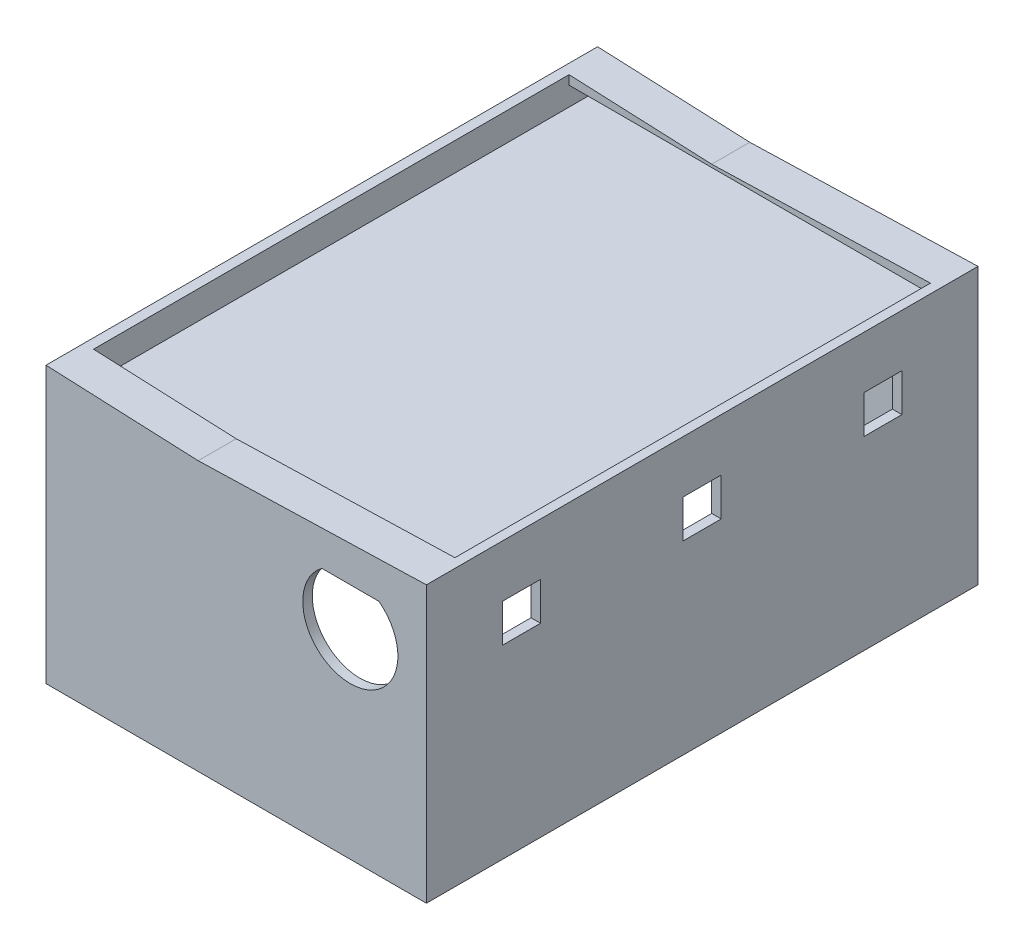
SolidWorks part; units mm, degrees
ref_plane "Front Plane" through (0, 0, 0) normal (0, 0, 1) x (1, 0, 0)
ref_plane "Top Plane" through (0, 0, 0) normal (0, 1, 0) x (1, 0, 0)
ref_plane "Right Plane" through (0, 0, 0) normal (1, 0, 0) x (0, 0, -1)
sketch "Sketch1" plane through (0, 0, 0) normal (0, 1, 0) x (1, 0, 0)
  line L1 (-96.0616, 57.1062) -> (103.9384, 57.1062)
  line L2 (-96.0616, 57.1062) -> (-96.0616, -232.8938)
  line L3 (-96.0616, -232.8938) -> (103.9384, -232.8938)
  line L4 (103.9384, 57.1062) -> (103.9384, -232.8938)
  dimension "D1" = 200
  dimension "D2" = 290
extrude "Boss-Extrude2" add sketch "Sketch1" along normal blind 10 contours L2 L3 L4 L1
sketch "Sketch2" plane through (0, 10, 0) normal (0, 1, 0) x (1, 0, 0)
  line L0 (-96.0616, -87.8938) -> (103.9384, -87.8938)
  line L1 (-96.0616, 57.1062) -> (-96.0616, -232.8938) construction
  line L2 (103.9384, 57.1062) -> (103.9384, -232.8938) construction
  line L3 (3.9384, 57.1062) -> (3.9384, -232.8938)
  line L4 (-96.0616, 57.1062) -> (103.9384, 57.1062) construction
  line L5 (-96.0616, -232.8938) -> (103.9384, -232.8938) construction
  line L7 (-91.0616, 52.1062) -> (98.9384, 52.1062)
  line L8 (-91.0616, 52.1062) -> (-91.0616, -227.8938)
  line L9 (-91.0616, -227.8938) -> (98.9384, -227.8938)
  line L10 (98.9384, 52.1062) -> (98.9384, -227.8938)
  line L11 (-91.0616, 52.1062) -> (98.9384, -227.8938) construction
  line L12 (-91.0616, -227.8938) -> (98.9384, 52.1062) construction
  point P12 (3.9384, -87.8938)
  line M3 (103.9384, 57.1062) -> (-96.0616, 57.1062)
  line M4 (-96.0616, 57.1062) -> (-96.0616, -232.8938)
  line M5 (-96.0616, -232.8938) -> (103.9384, -232.8938)
  line M6 (103.9384, -232.8938) -> (103.9384, 57.1062)
  dimension "D1" = 5
  dimension "D2" = 5
extrude "Boss-Extrude4" add sketch "Sketch2" along normal blind 140 contours L8 L7 L3 L0 M3 M4 | L7 L10 L0 L3 M6 M3 | L0 L10 L9 L3 M5 M6 | L9 L8 L0 L3 M4 M5
sketch "Sketch5" plane through (103.9384, 0, 0) normal (1, 0, 0) x (0, 0, -1)
  line L0 (-232.8938, 75) -> (-232.8938, 112.5)
  line L1 (-232.8938, 150) -> (-232.8938, 0) construction
  line L2 (-232.8938, 112.5) -> (57.1062, 112.5)
  line L3 (57.1062, 150) -> (57.1062, 0) construction
  line L4 (-87.8938, 112.5) -> (-160.3938, 112.5)
  line L5 (-87.8938, 112.5) -> (7.1062, 112.5)
  line L7 (-192.8938, 122.5) -> (-172.8938, 122.5)
  line L8 (-192.8938, 122.5) -> (-192.8938, 102.5)
  line L9 (-192.8938, 102.5) -> (-172.8938, 102.5)
  line L10 (-172.8938, 122.5) -> (-172.8938, 102.5)
  line L11 (-192.8938, 122.5) -> (-172.8938, 102.5) construction
  line L12 (-192.8938, 102.5) -> (-172.8938, 122.5) construction
  line L13 (-97.8938, 122.5) -> (-77.8938, 122.5)
  line L14 (-97.8938, 122.5) -> (-97.8938, 102.5)
  line L15 (-97.8938, 102.5) -> (-77.8938, 102.5)
  line L16 (-77.8938, 122.5) -> (-77.8938, 102.5)
  line L17 (-97.8938, 122.5) -> (-77.8938, 102.5) construction
  line L18 (-97.8938, 102.5) -> (-77.8938, 122.5) construction
  line L19 (-2.8938, 122.5) -> (17.1062, 122.5)
  line L20 (-2.8938, 122.5) -> (-2.8938, 102.5)
  line L21 (-2.8938, 102.5) -> (17.1062, 102.5)
  line L22 (17.1062, 122.5) -> (17.1062, 102.5)
  line L23 (-2.8938, 122.5) -> (17.1062, 102.5) construction
  line L24 (-2.8938, 102.5) -> (17.1062, 122.5) construction
  point P9 (-182.8938, 112.5)
  point P23 (0, 0)
  point P24 (0, 0)
  dimension "D1" = 37.5
  dimension "D2" = 75
  dimension "D4" = 20
  dimension "D5" = 20
  dimension "D6" = 20
  dimension "D7" = 20
  dimension "D8" = 20
  dimension "D9" = 20
  dimension "D10" = 75
extrude "Cut-Extrude1" cut sketch "Sketch5" against normal blind 10 contours L19 L22 L21 L20 | L13 L16 L15 L14 | L7 L10 L9 L8
sketch "Sketch6" plane through (-96.0616, 0, 0) normal (-1, 0, 0) x (0, 0, 1)
  line L0 (87.8938, 150) -> (87.8938, 0)
  line L1 (-57.1062, 150) -> (232.8938, 150) construction
  line L2 (-57.1062, 0) -> (232.8938, 0) construction
  line L3 (232.8938, 150) -> (194.2563, 150)
  line L4 (-57.1062, 150) -> (-18.4687, 150)
  line L5 (194.2563, 150) -> (194.2563, 0)
  line L6 (-18.4687, 150) -> (-18.4687, 0)
  line L7 (-18.4687, 75) -> (-18.4687, 150)
  line L8 (194.2563, 150) -> (194.2563, 75)
  line L9 (194.2563, 150) -> (194.2563, 112.5)
  line L10 (-18.4687, 150) -> (-18.4687, 112.5)
  line L11 (194.2563, 112.5) -> (-18.4687, 112.5)
  line L12 (194.2563, 112.5) -> (185.4763, 112.5)
  line L13 (-18.4687, 112.5) -> (-9.6887, 112.5)
  line L14 (-9.6887, 112.5) -> (-9.6887, 61.57)
  line L15 (185.4763, 112.5) -> (185.4763, 61.57)
  circle A0 centre (185.4763, 112.5) radius 3.78
  circle A1 centre (-9.6887, 112.5) radius 3.78
  circle A2 centre (185.4763, 61.57) radius 3.78
  circle A3 centre (-9.6887, 61.57) radius 3.78
  dimension "D7" = 7.56
  dimension "D8" = 7.56
  dimension "D11" = 7.56
  dimension "D12" = 7.56
  dimension "D1" = 38.6375
  dimension "D2" = 38.6375
  dimension "D3" = 37.5
  dimension "D4" = 37.5
  dimension "D5" = 8.78
  dimension "D6" = 8.78
  dimension "D9" = 50.93
  dimension "D10" = 50.93
extrude "Cut-Extrude2" cut sketch "Sketch6" against normal blind 10 contours A0 | A2 | A3 | A1
sketch "Sketch7" plane through (0, 0, 232.8938) normal (0, 0, 1) x (1, 0, 0)
  line L0 (103.9384, 150) -> (103.9384, 0) construction
  line L1 (-96.0616, 150) -> (103.9384, 150) construction
  circle A0 centre (63.9384, 110) radius 25
  dimension "D1" = 50
  dimension "D2" = 40
  dimension "D3" = 40
extrude "Cut-Extrude3" cut sketch "Sketch7" against normal blind 10 contours A0
sketch "Sketch8" plane through (0, 10, 0) normal (0, 1, 0) x (1, 0, 0)
  line L1 (-91.0616, 52.1062) -> (98.9384, 52.1062)
  line L2 (-91.0616, 52.1062) -> (-91.0616, -227.8938)
  line L3 (-91.0616, -227.8938) -> (98.9384, -227.8938)
  line L4 (98.9384, 52.1062) -> (98.9384, -227.8938)
extrude "Cut-Extrude4" cut sketch "Sketch8" against normal blind 10
sketch "Sketch9" plane through (0, 0, 0) normal (0, -1, 0) x (1, 0, 0)
  line L1 (-102.3219, 239.6938) -> (109.1358, 239.6938)
  line L2 (-102.3219, 239.6938) -> (-102.3219, -61.6829)
  line L3 (-102.3219, -61.6829) -> (109.1358, -61.6829)
  line L4 (109.1358, 239.6938) -> (109.1358, -61.6829)
extrude "Cut-Extrude5" cut sketch "Sketch9" against normal blind 5
sketch "Sketch10" plane through (0, 0, 227.8938) normal (0, 0, -1) x (-1, 0, 0)
  line L0 (96.0616, 150) -> (96.0616, 5) construction
  line L1 (-103.9384, 150) -> (96.0616, 150)
  line L2 (-103.9384, 150) -> (-103.9384, 145)
  line L3 (-103.9384, 145) -> (96.0616, 145)
  line L4 (96.0616, 150) -> (96.0616, 145)
  dimension "D1" = 5
extrude "Boss-Extrude7" add sketch "Sketch10" along normal blind 15 contours L1 L4 L3 L2
sketch "Sketch12" plane through (0, 0, -52.1062) normal (0, 0, 1) x (1, 0, 0)
  line L0 (103.9384, 150) -> (103.9384, 5) construction
  line L1 (-96.0616, 150) -> (103.9384, 150)
  line L2 (-96.0616, 150) -> (-96.0616, 145)
  line L3 (-96.0616, 145) -> (103.9384, 145)
  line L4 (103.9384, 150) -> (103.9384, 145)
  point P7 (0, 0)
  dimension "D1" = 5
extrude "Boss-Extrude8" add sketch "Sketch12" along normal blind 15
sketch "Sketch13" plane through (-91.0616, 0, 0) normal (1, 0, 0) x (0, 0, -1)
  line L0 (-232.8938, 150) -> (-232.8938, 5) construction
  line L1 (-232.8938, 135) -> (57.1062, 135)
  line L2 (-232.8938, 135) -> (-232.8938, 130)
  line L3 (-232.8938, 130) -> (57.1062, 130)
  line L4 (57.1062, 135) -> (57.1062, 130)
  line L5 (57.1062, 150) -> (57.1062, 5) construction
  line L6 (-232.8938, 150) -> (57.1062, 150) construction
  dimension "D1" = 5
  dimension "D2" = 15
extrude "Boss-Extrude14" add sketch "Sketch13" along normal blind 190 contours L1 L4 L3 L2
sketch "Sketch17" plane through (0, 0, 232.8938) normal (0, 0, 1) x (1, 0, 0)
  line L0 (-96.0616, 150) -> (-16.0616, 150)
  line L1 (-96.0616, 150) -> (103.9384, 150) construction
  line L2 (-16.0616, 150) -> (-16.0616, 146.51)
  line L3 (-16.0616, 146.51) -> (-96.0616, 150)
  line L4 (-16.0616, 146.51) -> (103.9384, 150)
  line L5 (103.9384, 150) -> (-96.0616, 150)
  line M7 (103.9384, 150) -> (-96.0616, 150)
  dimension "D1" = 80
  dimension "D2" = 3.49
extrude "Cut-Extrude6" cut sketch "Sketch17" against normal blind 300 contours L3 L2 M7 | L2 L4 M7
